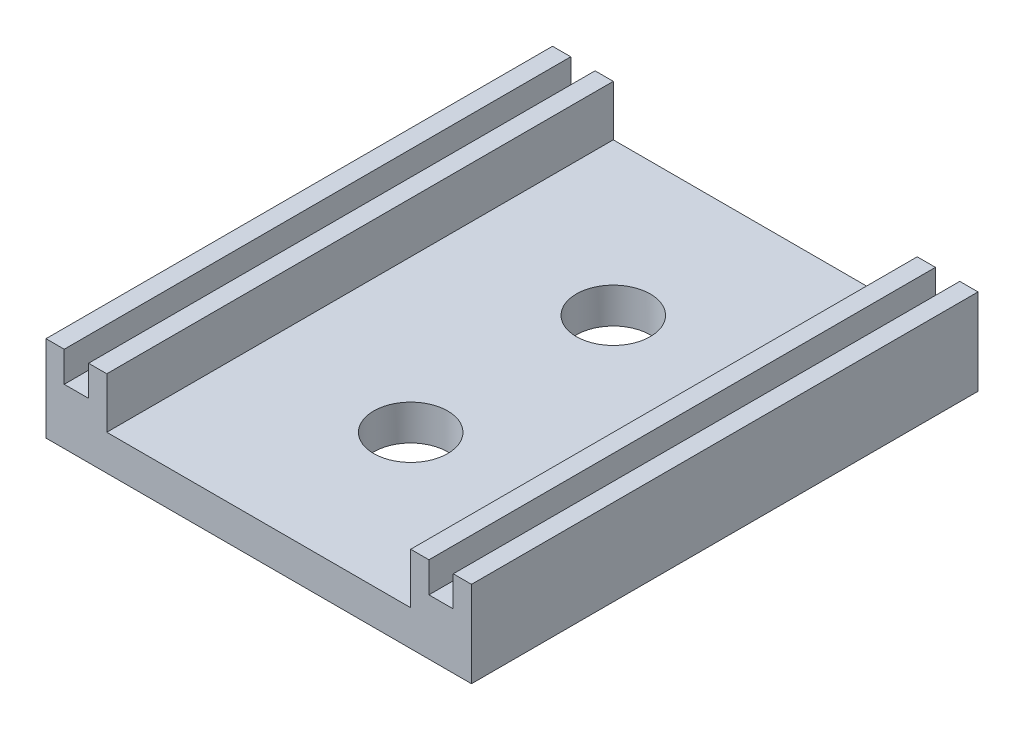
SolidWorks part; units mm, degrees
ref_plane "Front Plane" through (0, 0, 0) normal (0, 0, 1) x (1, 0, 0)
ref_plane "Top Plane" through (0, 0, 0) normal (0, 1, 0) x (1, 0, 0)
ref_plane "Right Plane" through (0, 0, 0) normal (1, 0, 0) x (0, 0, -1)
sketch "Sketch1" plane through (0, 0, 0) normal (0, 1, 0) x (1, 0, 0)
  line L1 (-20, -25) -> (20, -25)
  line L2 (-20, -25) -> (-20, 25)
  line L3 (-20, 25) -> (20, 25)
  line L4 (20, -25) -> (20, 25)
  line L5 (-20, -25) -> (20, 25) construction
  line L6 (-20, 25) -> (20, -25) construction
  point P0 (0, 0)
  dimension "D1" = 40
  dimension "D2" = 50
extrude "Boss-Extrude1" add sketch "Sketch1" along normal blind 3.5
sketch "Sketch2" plane through (0, 3.5, 0) normal (0, 1, 0) x (1, 0, 0)
  line L0 (20, -25) -> (20, 25) construction
  line L1 (-20, 25) -> (20, 25)
  line L2 (-20, 25) -> (-20, 21)
  line L3 (-20, 21) -> (20, 21)
  line L4 (20, 25) -> (20, 21)
  dimension "D1" = 4
extrude "Boss-Extrude2" add sketch "Sketch2" along normal blind 5
sketch "Sketch3" plane through (0, 3.5, 0) normal (0, 1, 0) x (1, 0, 0)
  line L0 (-20, 21) -> (20, 21) construction
  line L1 (-20, -25) -> (-16, -25)
  line L2 (-20, -25) -> (-20, 21)
  line L3 (-20, 21) -> (-16, 21)
  line L4 (-16, -25) -> (-16, 21)
  dimension "D1" = 4
extrude "Boss-Extrude3" add sketch "Sketch3" along normal blind 5
sketch "Sketch4" plane through (0, 8.5, 0) normal (0, 1, 0) x (1, 0, 0)
  line L0 (-16, 21) -> (-20, 21) construction
  line L2 (-18, 23.7623) -> (-18, -25) construction
  line L3 (-20, -25) -> (-16, -25) construction
  line L4 (20, 25) -> (-20, 25) construction
  line L5 (-19.2, -25) -> (-16.8, -25)
  line L6 (-19.2, -25) -> (-19.2, 25)
  line L7 (-19.2, 25) -> (-16.8, 25)
  line L8 (-16.8, -25) -> (-16.8, 25)
  dimension "D1" = 2.4
extrude "Cut-Extrude1" cut sketch "Sketch4" against normal blind 3
mirror "Mirror1" about plane through (0, 0, 0) normal (1, 0, 0) of "Cut-Extrude1", "Boss-Extrude3"
ref_plane "Plane1" through (0, 0, -2.23) normal (0, 0, 1) x (1, 0, 0)
sketch "Sketch18" plane through (-20, 0, 0) normal (-1, 0, 0) x (0, 0, 1)
  line L1 (-25, 8.5) -> (25, 8.5)
  line L2 (-25, 8.5) -> (-25, 0)
  line L3 (-25, 0) -> (25, 0)
  line L4 (25, 8.5) -> (25, 0)
extrude "Boss-Extrude8" add sketch "Sketch18" along normal blind 1
mirror "Mirror5" about plane through (0, 0, 0) normal (1, 0, 0) of "Boss-Extrude8"
sketch "Sketch19" plane through (0, 3.5, 0) normal (0, 1, 0) x (1, 0, 0)
  line L0 (-16, -25) -> (16, -25) construction
  circle A0 centre (0, -10) radius 3.65
  circle A1 centre (0, 10) radius 3.65
  dimension "D3" = 7.3
  dimension "D4" = 7.3
  dimension "D1" = 15
  dimension "D2" = 35
extrude "Cut-Extrude2" cut sketch "Sketch19" against normal through all both and the other way through all
sketch "Sketch20" plane through (0, 8.5, 0) normal (0, 1, 0) x (1, 0, 0)
  line L0 (-16, 21) -> (16, 21)
  line L1 (-16, 21) -> (-16, 25)
  line L2 (16, 21) -> (16, 25)
  line L3 (-16, 25) -> (16, 25)
  line L4 (16.8, 25) -> (-16.8, 25) construction
extrude "Cut-Extrude3" cut sketch "Sketch20" against normal up to surface (5 mm away) up to face at (0, 3.5, 6.35)
sketch "Sketch21" plane through (-16, 0, 0) normal (1, 0, 0) x (0, 0, -1)
  line L1 (-25, 8.5) -> (25, 8.5)
  line L2 (-25, 8.5) -> (-25, 3.5)
  line L3 (-25, 3.5) -> (25, 3.5)
  line L4 (25, 8.5) -> (25, 3.5)
extrude "Boss-Extrude9" add sketch "Sketch21" along normal blind 1
mirror "Mirror6" about plane through (0, 0, 0) normal (1, 0, 0) of "Boss-Extrude9"
